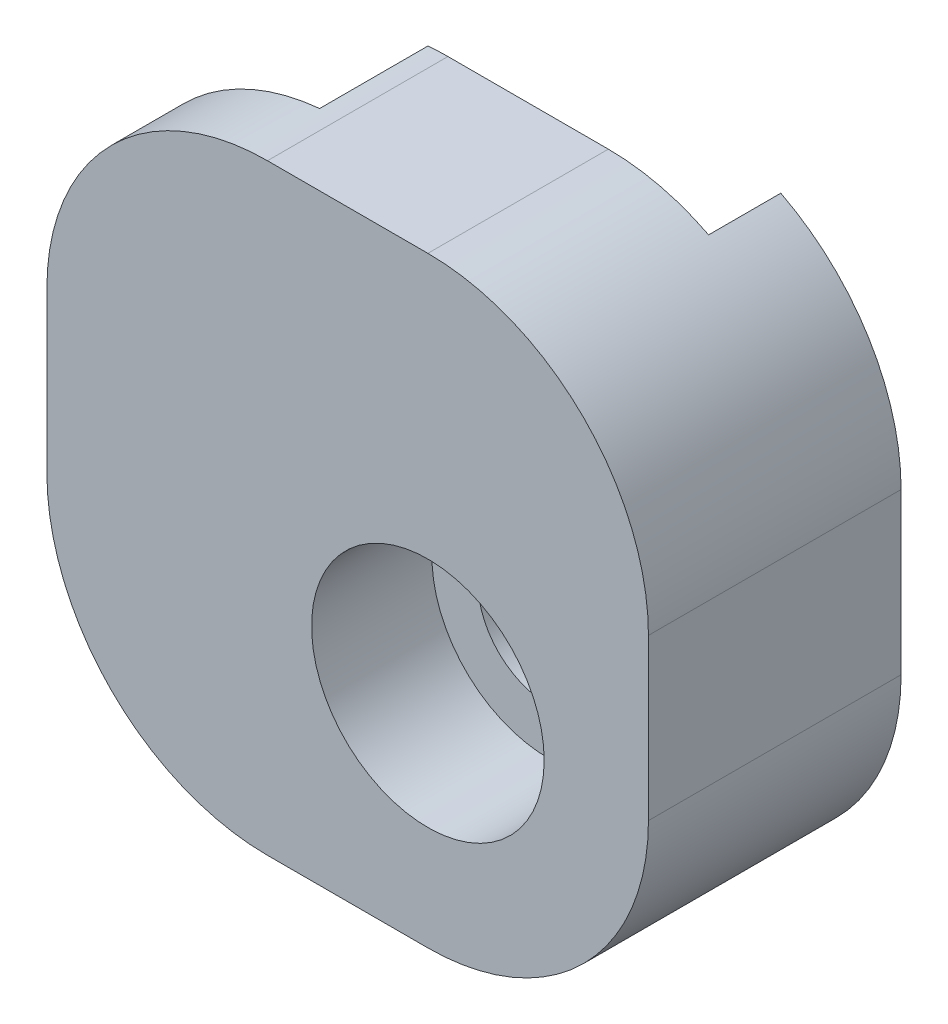
SolidWorks part; units mm, degrees
ref_plane "Plano frontal" through (0, 0, 0) normal (0, 0, 1) x (1, 0, 0)
ref_plane "Plano superior" through (0, 0, 0) normal (0, 1, 0) x (1, 0, 0)
ref_plane "Plano direito" through (0, 0, 0) normal (1, 0, 0) x (0, 0, -1)
sketch "Esboço3" plane through (0, 0, 0) normal (0, 0, 1) x (1, 0, 0)
  line L0 (0, 0) -> (-2.5, 2.5) construction
  line L1 (0, 0) -> (-7, 0)
  line L2 (0, 0) -> (0, 12)
  line L3 (0, 12) -> (-7, 12)
  line L4 (-7, 0) -> (-7, 12)
  circle A0 centre (-2.5, 2.5) radius 1.75
  dimension "D5" = 3.5
  dimension "D1" = 12
  dimension "D2" = 7
  dimension "D3" = 2.5
  dimension "D4" = 2.5
extrude "Ressalto-extrusão2" add sketch "Esboço3" along normal blind 2.7
sketch "Esboço4" plane through (0, 0, 2.7) normal (0, 0, 1) x (1, 0, 0)
  line L4 (0, 0) -> (0, 12)
  line L5 (0, 12) -> (-7, 12)
  line L6 (-7, 12) -> (-7, 0)
  line L7 (-7, 0) -> (0, 0)
  line L8 (0, 0) -> (0, 12)
  line L9 (0, 12) -> (-7, 12)
  line L10 (-7, 12) -> (-7, 0)
  line L11 (-7, 0) -> (0, 0)
  circle A0 centre (-2.5, 2.5) radius 1.75 construction
  circle A1 centre (-2.5, 2.5) radius 1.75
  dimension "D1" = 0
extrude "Ressalto-extrusão3" add sketch "Esboço4" along normal blind 2.1
sketch "Esboço5" plane through (-7, 0, 0) normal (-1, 0, 0) x (0, 0, 1)
  line L0 (4.8, 12) -> (4.8, 0) construction
  line L1 (4.8, 12) -> (4.8, 0)
  line L2 (2.7, 12) -> (2.7, 0)
  line L3 (4.8, 12) -> (2.7, 12)
  line L4 (2.7, 0) -> (4.8, 0)
  dimension "D1" = 2.1
extrude "Ressalto-extrusão4" add sketch "Esboço5" along normal blind 5
sketch "Esboço6" plane through (0, 0, 0) normal (0, -1, 0) x (1, 0, 0)
  line L6 (-7, 0) -> (0, 0)
  line L7 (0, 0) -> (0, 4.8)
  line L8 (0, 4.8) -> (-12, 4.8)
  line L9 (-12, 4.8) -> (-12, 2.7)
  line L10 (-12, 2.7) -> (-7, 2.7)
  line L11 (-7, 2.7) -> (-7, 0)
  line L12 (-7, 0) -> (0, 0)
  line L13 (0, 0) -> (0, 4.8)
  line L14 (0, 4.8) -> (-12, 4.8)
  line L15 (-12, 4.8) -> (-12, 2.7)
  line L16 (-12, 2.7) -> (-7, 2.7)
  line L17 (-7, 2.7) -> (-7, 0)
  dimension "D1" = 0
extrude "Ressalto-extrusão5" add sketch "Esboço6" along normal blind 3
sketch "Esboço7" plane through (0, 0, 0) normal (1, 0, 0) x (0, 0, -1)
  line L4 (0, -3) -> (0, 12)
  line L5 (0, 12) -> (-4.8, 12)
  line L6 (-4.8, 12) -> (-4.8, -3)
  line L7 (-4.8, -3) -> (0, -3)
  line L8 (0, -3) -> (0, 12)
  line L9 (0, 12) -> (-4.8, 12)
  line L10 (-4.8, 12) -> (-4.8, -3)
  line L11 (-4.8, -3) -> (0, -3)
  dimension "D1" = 0
extrude "Ressalto-extrusão6" add sketch "Esboço7" along normal blind 3
sketch "Esboço8" plane through (0, 0, 4.8) normal (0, 0, 1) x (1, 0, 0)
  circle A0 centre (-2.5, 2.5) radius 2.9
  dimension "D1" = 5.8
extrude "Corte-extrusão1" cut sketch "Esboço8" against normal blind 3
fillet "Filete1" radius 5.5 1 edges at (3, -3, 2.4)
sketch "Esboço10" plane through (0, 0, 0) normal (0, 0, -1) x (-1, 0, 0)
  line L0 (2.5, 2.5) -> (0, 0) construction
  line L1 (7, 12) -> (7, -3) construction
  line L2 (0, 0) -> (7, 0)
  line L3 (0, 0) -> (0, 14)
  line L4 (0, 14) -> (7, 14)
  line L5 (7, 0) -> (7, 14)
  line L6 (7, 12) -> (7, -3) construction
  line L7 (7, -3) -> (2.5, -3) construction
  line L8 (-3, 2.5) -> (-3, 12) construction
  line L9 (-3, 12) -> (7, 12) construction
  line L10 (7, -3) -> (2.5, -3)
  line L11 (-3, 2.5) -> (-3, 12)
  line L12 (-3, 12) -> (7, 12)
  line L13 (7, 12) -> (7, -3)
  arc A0 (-3, 2.5) -> (2.5, -3) centre (2.5, 2.5) ccw construction
  arc A1 (-3, 2.5) -> (2.5, -3) centre (2.5, 2.5) ccw
  line M10 (-3, 12) -> (-3, 2.5)
  arc M11 (-3, 2.5) -> (2.5, -3) centre (2.5, 2.5) ccw
  line M12 (2.5, -3) -> (7, -3)
  line M13 (7, -3) -> (7, 12)
  line M14 (7, 12) -> (-3, 12)
  dimension "D1" = 2.5
  dimension "D2" = 2.5
extrude "Ressalto-extrusão7" add sketch "Esboço10" along normal blind 1.5 contours L2 L3 M14 M10 M11 M12 M13
sketch "Esboço13" plane through (0, 0, 4.8) normal (0, 0, 1) x (1, 0, 0)
  line L0 (-2.5, -3) -> (-12, -3) construction
  line L1 (-12, -3) -> (-12, 12) construction
  line L6 (-12, -3) -> (-2.5, -3)
  line L7 (3, 2.5) -> (3, 12)
  line L8 (3, 12) -> (-12, 12)
  line L9 (-12, 12) -> (-12, -3)
  line L10 (-12, -3) -> (-6.5, -3)
  line L13 (-12, 2.5) -> (-12, -3)
  arc A0 (-12, 2.5) -> (-6.5, -3) centre (-6.5, 2.5) ccw
  arc A2 (-2.5, -3) -> (3, 2.5) centre (-2.5, 2.5) ccw
  dimension "D1" = 11
  dimension "D2" = 0
sketch "Esboço14" plane through (0, 0, 4.8) normal (0, 0, 1) x (1, 0, 0)
  line L4 (-12, -3) -> (-2.5, -3)
  line L5 (3, 2.5) -> (3, 12)
  line L6 (3, 12) -> (-12, 12)
  line L7 (-12, 12) -> (-12, -3)
  line L8 (-12, -3) -> (-2.5, -3)
  line L9 (3, 2.5) -> (3, 6.5)
  line L10 (-2.5, 12) -> (-6.5, 12)
  line L11 (-12, 6.5) -> (-12, -3)
  line L16 (3, 12) -> (3, 2.5) construction
  line L17 (-12, -3) -> (-12, 12) construction
  line L18 (3, 12) -> (-12, 12) construction
  line L19 (3, 12) -> (3, 2.5)
  line L20 (-12, -3) -> (-12, 12)
  line L21 (3, 12) -> (-12, 12)
  arc A0 (-12, 6.5) -> (-6.5, 12) centre (-6.5, 6.5) cw
  arc A1 (-2.5, 12) -> (3, 6.5) centre (-2.5, 6.5) cw
  arc A3 (-2.5, -3) -> (3, 2.5) centre (-2.5, 2.5) ccw
  arc A5 (-2.5, -3) -> (3, 2.5) centre (-2.5, 2.5) ccw
  line M15 (3, 2.5) -> (3, 12)
  line M16 (3, 12) -> (-12, 12)
  line M17 (-12, 12) -> (-12, -3)
  dimension "D2" = 5.5
  dimension "D1" = 0
extrude "Corte-extrusão4" cut sketch "Esboço14" against normal up to surface (6.3 mm away) contours A0 M17 M16 | A1 M16 M15 up to face at (-1.3373, 2.7658, -1.5)
extrude "Corte-extrusão5" cut sketch "Esboço13" against normal up to surface (6.3 mm away) contours A0 L10 L13 up to face at (-1.2386, 1.9547, -1.5)
sketch "Esboço15" plane through (0, 0, -1.5) normal (0, 0, -1) x (-1, 0, 0)
  line L5 (2.5, -3) -> (6.5, -3)
  line L6 (7, -2.9772) -> (7, 0)
  line L7 (7, 0) -> (0, 0)
  line L8 (0, 0) -> (0, 11.399)
  line L9 (-3, 6.5) -> (-3, 2.5)
  line L10 (2.5, -3) -> (6.5, -3)
  line L11 (7, -2.9772) -> (7, 0)
  line L12 (7, 0) -> (0, 0)
  line L13 (0, 0) -> (0, 11.399)
  line L14 (-3, 6.5) -> (-3, 2.5)
  arc A3 (6.5, -3) -> (7, -2.9772) centre (6.5, 2.5) ccw
  arc A4 (0, 11.399) -> (-3, 6.5) centre (2.5, 6.5) ccw
  arc A5 (-3, 2.5) -> (2.5, -3) centre (2.5, 2.5) ccw
  arc A6 (6.5, -3) -> (7, -2.9772) centre (6.5, 2.5) ccw
  arc A7 (0, 11.399) -> (-3, 6.5) centre (2.5, 6.5) ccw
  arc A8 (-3, 2.5) -> (2.5, -3) centre (2.5, 2.5) ccw
  dimension "D1" = 0
extrude "Ressalto-extrusão8" add sketch "Esboço15" along normal blind 0.3
sketch "Esboço16" plane through (0, 0, 4.8) normal (0, 0, 1) x (1, 0, 0)
  line L4 (-12, 6.5) -> (-12, 2.5)
  line L5 (-6.5, -3) -> (-2.5, -3)
  line L6 (3, 2.5) -> (3, 6.5)
  line L7 (-2.5, 12) -> (-6.5, 12)
  line L8 (-12, 6.5) -> (-12, 2.5)
  line L9 (-6.5, -3) -> (-2.5, -3)
  line L10 (3, 2.5) -> (3, 6.5)
  line L11 (-2.5, 12) -> (-6.5, 12)
  arc A4 (-12, 2.5) -> (-6.5, -3) centre (-6.5, 2.5) ccw
  arc A5 (-2.5, -3) -> (3, 2.5) centre (-2.5, 2.5) ccw
  arc A6 (3, 6.5) -> (-2.5, 12) centre (-2.5, 6.5) ccw
  arc A7 (-6.5, 12) -> (-12, 6.5) centre (-6.5, 6.5) ccw
  arc A8 (-12, 2.5) -> (-6.5, -3) centre (-6.5, 2.5) ccw
  arc A9 (-2.5, -3) -> (3, 2.5) centre (-2.5, 2.5) ccw
  arc A10 (3, 6.5) -> (-2.5, 12) centre (-2.5, 6.5) ccw
  arc A11 (-6.5, 12) -> (-12, 6.5) centre (-6.5, 6.5) ccw
  dimension "D1" = 0
extrude "Corte-extrusão6" cut sketch "Esboço16" against normal blind 0.3
sketch "Esboço17" plane through (0, 0, 1.8) normal (0, 0, 1) x (1, 0, 0)
  circle A1 centre (-2.5, 2.5) radius 2.9
  circle A2 centre (-2.5, 2.5) radius 2.9
  dimension "D1" = 0
extrude "Corte-extrusão7" cut sketch "Esboço17" against normal blind 0.3
